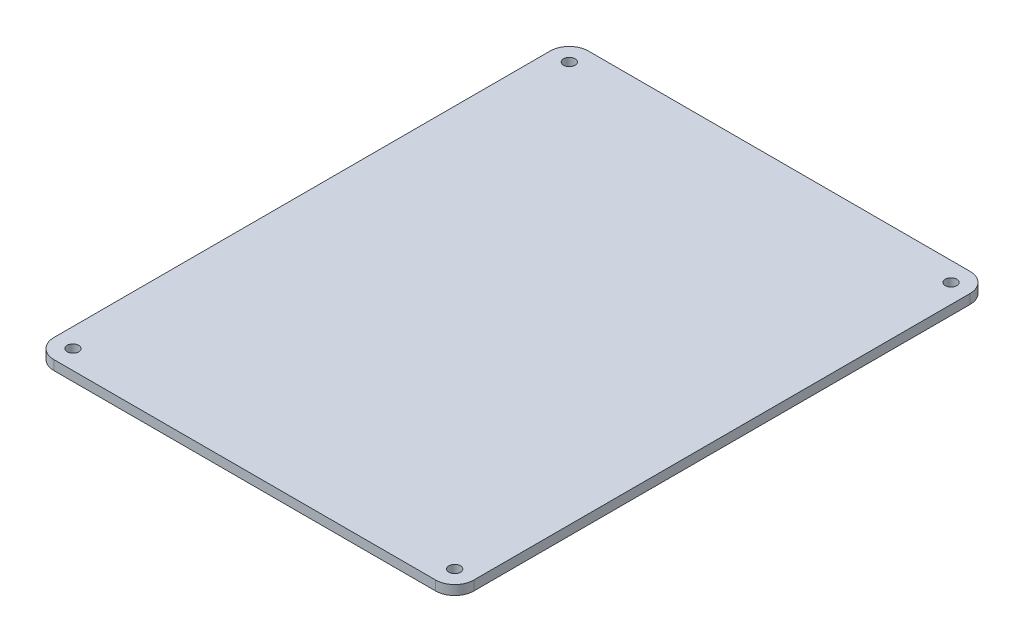
SolidWorks part; units mm, degrees
ref_plane "前视基准面" through (0, 0, 0) normal (0, 0, 1) x (1, 0, 0)
ref_plane "上视基准面" through (0, 0, 0) normal (0, 1, 0) x (1, 0, 0)
ref_plane "右视基准面" through (0, 0, 0) normal (1, 0, 0) x (0, 0, -1)
sketch "草图1" plane through (0, 177.1371, 0) normal (0, 1, 0) x (1, 0, 0)
  line L1 (-133.0995, -1.7273) -> (-33.0995, -1.7273)
  line L2 (-138.0995, -6.7273) -> (-138.0995, -136.7273)
  line L3 (-133.0995, -141.7273) -> (-33.0995, -141.7273)
  line L4 (-28.0995, -6.7273) -> (-28.0995, -136.7273)
  arc A4 (-133.0995, -141.7273) -> (-138.0995, -136.7273) centre (-133.0995, -136.7273) cw
  arc A5 (-33.0995, -141.7273) -> (-28.0995, -136.7273) centre (-33.0995, -136.7273) ccw
  arc A6 (-28.0995, -6.7273) -> (-33.0995, -1.7273) centre (-33.0995, -6.7273) ccw
  arc A7 (-138.0995, -6.7273) -> (-133.0995, -1.7273) centre (-133.0995, -6.7273) cw
  circle A8 centre (-133.0995, -6.7273) radius 1.5
  circle A9 centre (-33.0995, -6.7273) radius 1.5
  circle A10 centre (-33.0995, -136.7273) radius 1.5
  circle A11 centre (-133.0995, -136.7273) radius 1.5
  dimension "D1" = 5
  dimension "D2" = 3
  dimension "D3" = 3
  dimension "D4" = 3
  dimension "D5" = 3
extrude "凸台-拉伸1" add sketch "草图1" along normal blind 2.5
ref_plane "基准面1" through (-83.0995, 0, 0) normal (1, 0, 0) x (0, 0, -1)
ref_plane "基准面2" through (0, 0, 71.7273) normal (0, 0, -1) x (-1, 0, 0)
